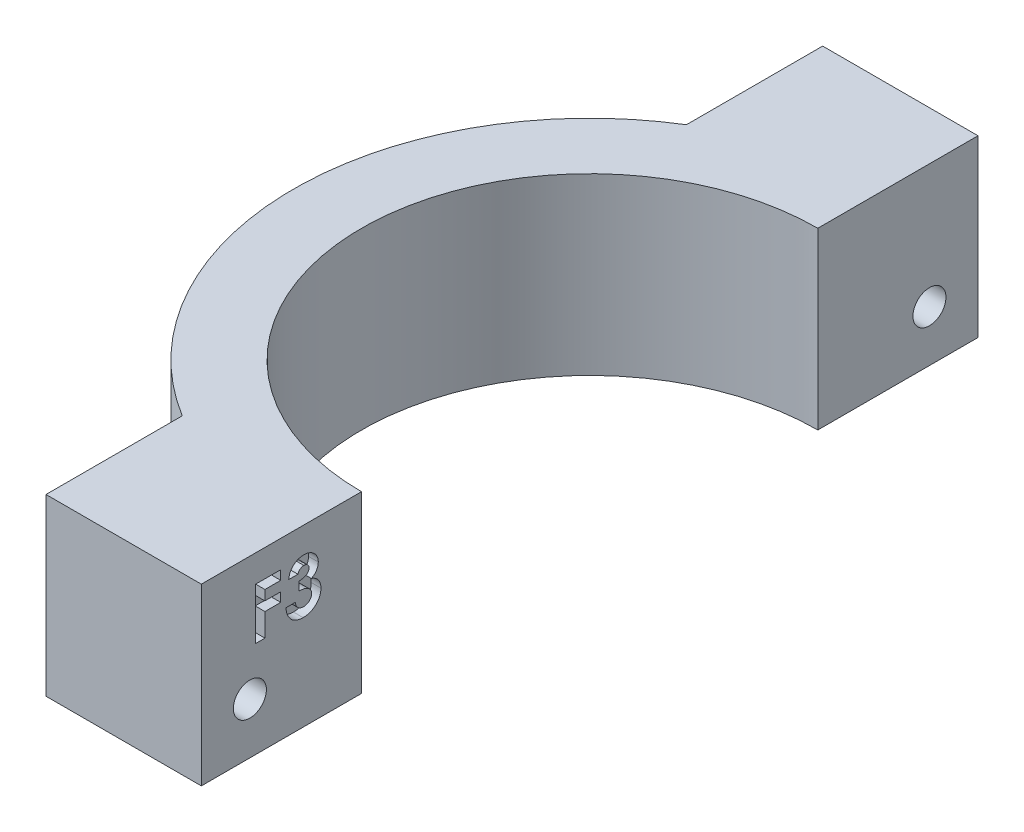
SolidWorks part; units mm, degrees
ref_plane "Front Plane" through (0, 0, 0) normal (0, 0, 1) x (1, 0, 0)
ref_plane "Top Plane" through (0, 0, 0) normal (0, 1, 0) x (1, 0, 0)
ref_plane "Right Plane" through (0, 0, 0) normal (1, 0, 0) x (0, 0, -1)
sketch "Sketch1" plane through (0, 0, 0) normal (0, 1, 0) x (1, 0, 0)
  line L0 (-48.9983, 32.5286) -> (-48.9983, -47.4714)
  line L1 (-48.9983, -47.4714) -> (-16.9983, -47.4714)
  line L2 (-16.9983, -47.4714) -> (-16.9983, -30.9714)
  line L3 (-48.9983, 32.5286) -> (-16.9983, 32.5286)
  line L4 (-16.9983, 32.5286) -> (-16.9983, 16.0286)
  line L5 (-32.9983, 32.5286) -> (-32.9983, 18.4949)
  line L6 (-32.9983, -47.4714) -> (-32.9983, -33.4378)
  arc A0 (-16.9983, 16.0286) -> (-16.9983, -30.9714) centre (-16.9983, -7.4714) ccw
  arc A1 (-16.9983, 23.0286) -> (-16.9983, -37.9714) centre (-16.9983, -7.4714) ccw
  point P14 (0, 0)
  point P15 (-32.5785, -30.9714)
  point P16 (-32.9983, -33.4378)
  dimension "D1" = 80
  dimension "D2" = 32
  dimension "D3" = 32
  dimension "D4" = 16.5
  dimension "D5" = 16.5
  dimension "D6" = 47
  dimension "D7" = 7
extrude "Boss-Extrude1" add sketch "Sketch1" along normal blind 18 contours A1 L4 L3 L5 | L4 A1 L0 L2 A0 | A1 L6 L1 L2
sketch "Sketch2" plane through (-16.9983, 0, 0) normal (1, 0, 0) x (0, 0, -1)
  line L0 (-47.4714, 18) -> (-47.4714, 0) construction
  line L3 (32.5286, 18) -> (32.5286, 0) construction
  line L8 (32.5286, 18) -> (16.0286, 18) construction
  line L9 (-47.4714, 18) -> (-30.9714, 18) construction
  circle A0 centre (-42.4714, 5.25) radius 1.7
  circle A1 centre (27.5286, 5.25) radius 1.7
  point P10 (0, 0)
  dimension "D3" = 12.75
  dimension "D1" = 5
  dimension "D2" = 5
  dimension "D4" = 12.75
extrude "Cut-Extrude1" cut sketch "Sketch2" against normal through all
sketch "Sketch3" plane through (-16.9983, 0, 0) normal (1, 0, 0) x (0, 0, -1)
  text T0 "<b>F3</b>" font "Century Gothic" height in points 20
extrude "Cut-Extrude2" cut sketch "Sketch3" against normal blind 1
sketch "Sketch4" plane through (-32.9983, 0, 0) normal (-1, 0, 0) x (0, 0, 1)
  line L1 (-25.5288, 2.7834) -> (-24.3925, 5.7486)
  line L2 (-24.3925, 5.7486) -> (-26.3923, 8.2152)
  line L3 (-26.3923, 8.2152) -> (-29.5284, 7.7166)
  line L4 (-29.5284, 7.7166) -> (-30.6646, 4.7514)
  line L5 (-30.6646, 4.7514) -> (-28.6648, 2.2848)
  line L6 (-28.6648, 2.2848) -> (-25.5288, 2.7834)
  line L7 (44.3628, 2.6993) -> (45.6261, 5.6126)
  line L8 (45.6261, 5.6126) -> (43.7347, 8.1633)
  line L9 (43.7347, 8.1633) -> (40.5801, 7.8007)
  line L10 (40.5801, 7.8007) -> (39.3168, 4.8874)
  line L11 (39.3168, 4.8874) -> (41.2081, 2.3367)
  line L12 (41.2081, 2.3367) -> (44.3628, 2.6993)
  circle A0 centre (-27.5286, 5.25) radius 2.75 construction
  circle A1 centre (42.4714, 5.25) radius 2.75 construction
extrude "Cut-Extrude3" cut sketch "Sketch4" against normal blind 5
